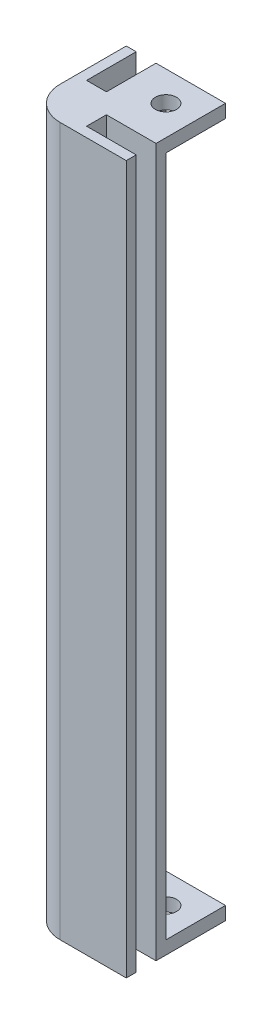
SolidWorks part; units mm, degrees
material "ABS"
ref_plane "Front Plane" through (0, 0, 0) normal (0, 0, 1) x (1, 0, 0)
ref_plane "Top Plane" through (0, 0, 0) normal (0, 1, 0) x (1, 0, 0)
ref_plane "Right Plane" through (0, 0, 0) normal (1, 0, 0) x (0, 0, -1)
sketch "Sketch4" plane through (0, 0, 0) normal (0, 1, 0) x (1, 0, 0)
  line L0 (-7.5, -7.5) -> (7.5, -7.5)
  line L1 (7.5, -7.5) -> (7.5, -6)
  line L2 (7.5, -6) -> (0, -6)
  line L3 (0, -6) -> (0, -3)
  line L4 (0, -3) -> (7.5, -3)
  line L5 (7.5, -3) -> (7.5, -1.5)
  line L6 (7.5, -1.5) -> (-1.5, -1.5)
  line L7 (-7.5, -7.5) -> (-7.5, 7.5)
  line L8 (-7.5, 7.5) -> (-6, 7.5)
  line L9 (-3, 7.5) -> (-1.5, 7.5)
  line L10 (-1.5, 7.5) -> (-1.5, -1.5)
  line L11 (-6, 7.5) -> (-6, 0)
  line L12 (-6, 0) -> (-3, 0)
  line L13 (-3, 0) -> (-3, 7.5)
  point P14 (0, -7.5)
  dimension "D1" = 15
  dimension "D2" = 1.5
  dimension "D3" = 9
  dimension "D4" = 3
  dimension "D5" = 7.5
  dimension "D6" = 7.5
  dimension "D7" = 7.5
  dimension "D8" = 7.5
  dimension "D9" = 6
extrude "Boss-Extrude1" add sketch "Sketch4" along normal blind 105
sketch "Sketch6" plane through (0, 0, 0) normal (0, -1, 0) x (1, 0, 0)
  line L0 (-7.5, 7.5) -> (7.5, 7.5)
  line L2 (-1.5, -7.5) -> (-7.5, -7.5)
  line L3 (-7.5, -7.5) -> (-7.5, 7.5)
  line L5 (7.5, 7.5) -> (7.5, 6)
  line L6 (7.5, 6) -> (0, 6)
  line L7 (0, 6) -> (0, 3)
  line L8 (0, 3) -> (7.5, 3)
  line L9 (7.5, 3) -> (7.5, 1.5)
  line L10 (7.5, 1.5) -> (-1.5, 1.5) construction
  line L11 (3, 1.5) -> (3, -3) construction
  line L12 (-1.5, -7.5) -> (-3, -7.5)
  line L13 (-3, -7.5) -> (-3, 0)
  line L14 (-3, 0) -> (-6, 0)
  line L15 (-6, 0) -> (-6, -7.5)
  line L16 (-6, -7.5) -> (-7.5, -7.5)
  line L17 (7.5, 1.5) -> (7.5, -7.5)
  line L18 (7.5, -7.5) -> (-1.5, -7.5)
  circle A0 centre (3, -3) radius 1.6
  dimension "D1" = 3.2
extrude "Boss-Extrude2" add sketch "Sketch6" along normal blind 2
fillet "Fillet3" radius 5 1 edges at (-7.5, 51.5, 7.5)
fillet "Fillet4" radius 2.5 1 edges at (-1.5, 52.5, 1.5)
sketch "Sketch7" plane through (0, 105, 0) normal (0, 1, 0) x (1, 0, 0)
  line L0 (-1.5, 7.5) -> (7.5, 7.5)
  line L1 (7.5, 7.5) -> (7.5, -1.5)
  line L2 (7.5, -1.5) -> (1, -1.5)
  line L3 (-1.5, 1) -> (-1.5, 7.5)
  arc A0 (1, -1.5) -> (-1.5, 1) centre (1, 1) cw
  circle A1 centre (3, 3) radius 1.6
  dimension "D1" = 3.2
extrude "Boss-Extrude3" add sketch "Sketch7" against normal blind 2
